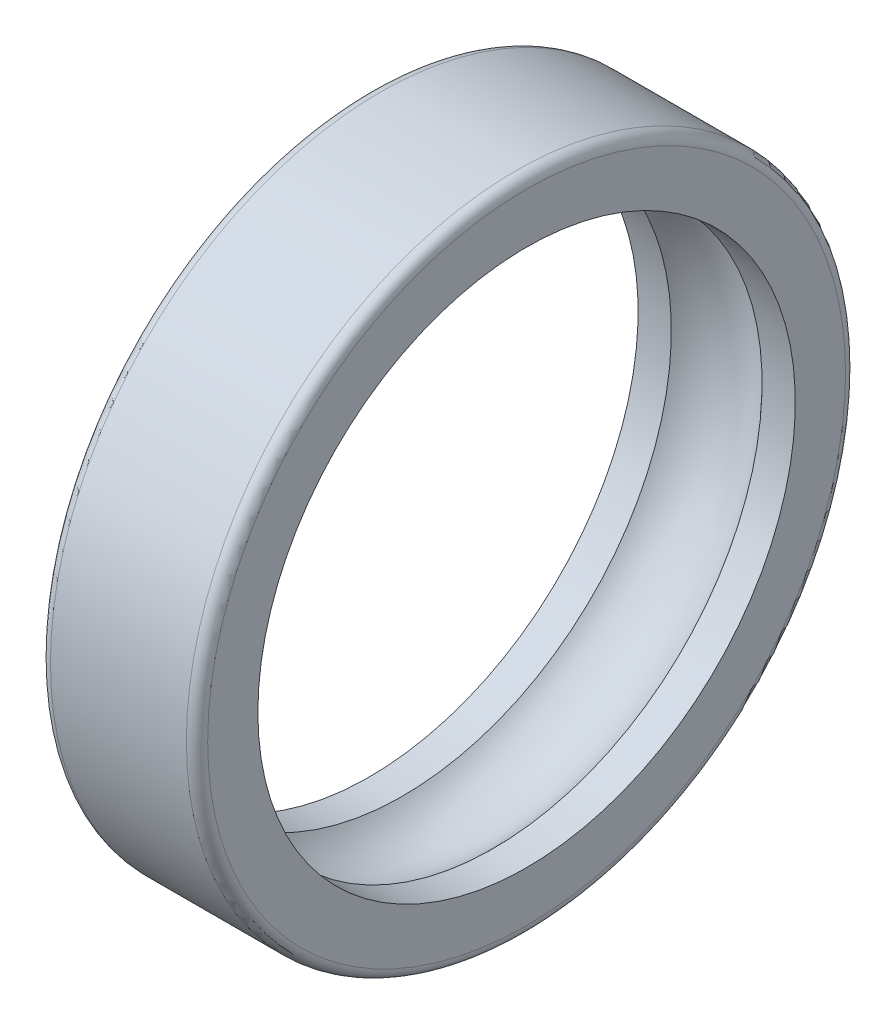
SolidWorks part; units mm, degrees
material "1060 Alloy"
ref_plane "Front Plane" through (0, 0, 0) normal (0, 0, 1) x (1, 0, 0)
ref_plane "Top Plane" through (0, 0, 0) normal (0, 1, 0) x (1, 0, 0)
ref_plane "Right Plane" through (0, 0, 0) normal (1, 0, 0) x (0, 0, -1)
sketch "Sketch3" plane through (0, 0, 0) normal (0, 0, 1) x (1, 0, 0)
  line L0 (-16.04, 0) -> (16.4174, 0) construction
  line L1 (0.1887, 53) -> (0, 0) construction
  line L2 (-15.3398, 53) -> (-8.7841, 53)
  line L3 (-15.3398, 53) -> (-15.3398, 65)
  line L4 (-15.3398, 65) -> (15.6602, 65)
  line L5 (15.6602, 53) -> (15.6602, 65)
  line L6 (-15.3398, 53) -> (15.6602, 65) construction
  line L7 (-15.3398, 65) -> (15.6602, 53) construction
  line L8 (9.1045, 53) -> (15.6602, 53)
  arc A0 (-8.7841, 53) -> (9.1045, 53) centre (0.1602, 45) cw
  point P3 (0.1602, 59)
  dimension "D5" = 12
  dimension "D1" = 31
  dimension "D2" = 65
  dimension "D3" = 53
  dimension "D4" = 8
revolve "Revolve1" add sketch "Sketch3" angle 360 about L0
fillet "Fillet1" radius 2.1 2 edges at (15.6602, 0, 65) (-15.3398, 0, 65)
